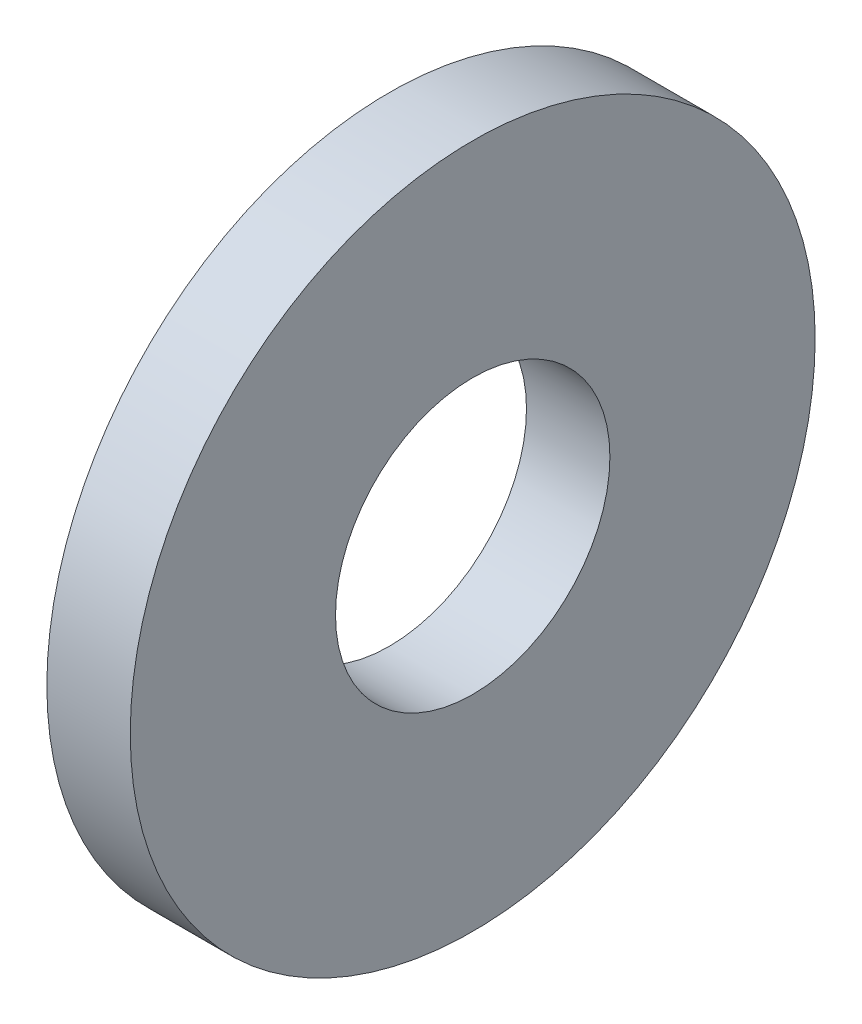
SolidWorks part; units mm, degrees
ref_plane "Front Plane" through (0, 0, 0) normal (0, 0, 1) x (1, 0, 0)
ref_plane "Top Plane" through (0, 0, 0) normal (0, 1, 0) x (1, 0, 0)
ref_plane "Right Plane" through (0, 0, 0) normal (1, 0, 0) x (0, 0, -1)
sketch "Sketch1" plane through (0, 0, 0) normal (1, 0, 0) x (0, 0, -1)
  circle A0 centre (0, 0) radius 3.9624
  circle A1 centre (0, 0) radius 1.5875
  dimension "OD" = 7.9248
  dimension "ID" = 3.175
extrude "Boss-Extrude1" add sketch "Sketch1" along normal blind 0.9652
